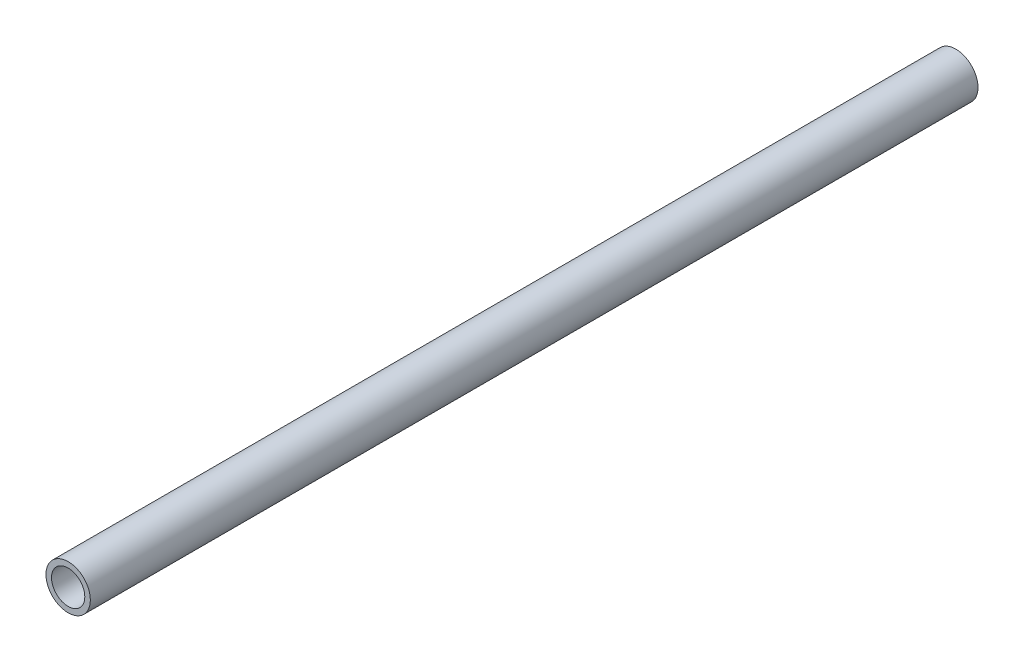
SolidWorks part; units mm, degrees
ref_plane "Plan de face" through (0, 0, 0) normal (0, 0, 1) x (1, 0, 0)
ref_plane "Plan de dessus" through (0, 0, 0) normal (0, 1, 0) x (1, 0, 0)
ref_plane "Plan de droite" through (0, 0, 0) normal (1, 0, 0) x (0, 0, -1)
sketch "Esquisse1" plane through (0, 0, 0) normal (0, 0, 1) x (1, 0, 0)
  circle A0 centre (0, 0) radius 4
  circle A1 centre (0, 0) radius 3
  dimension "D1" = 8
  dimension "D2" = 1
extrude "Boss.-Extru.1" add sketch "Esquisse1" along normal blind 160
